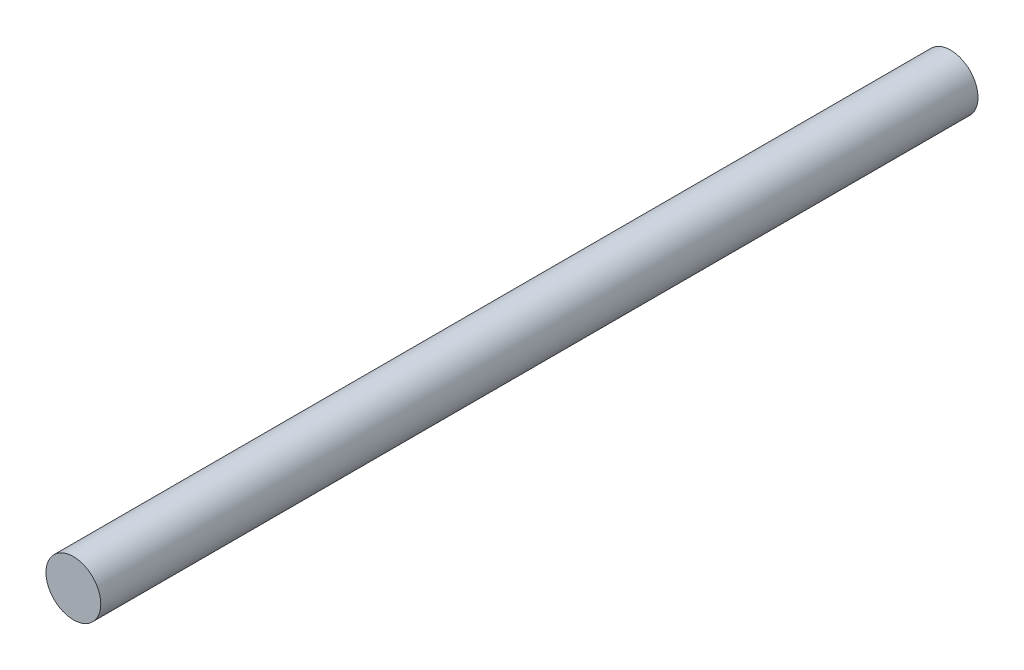
SolidWorks part; units mm, degrees
ref_plane "Front Plane" through (0, 0, 0) normal (0, 0, 1) x (1, 0, 0)
ref_plane "Top Plane" through (0, 0, 0) normal (0, 1, 0) x (1, 0, 0)
ref_plane "Right Plane" through (0, 0, 0) normal (1, 0, 0) x (0, 0, -1)
sketch "Sketch1" plane through (0, 0, 0) normal (0, 0, 1) x (1, 0, 0)
  circle A0 centre (2.8315, 2.8005) radius 1.5875
  dimension "D1" = 3.175
extrude "Boss-Extrude1" add sketch "Sketch1" along normal blind 50.8 contours A0
